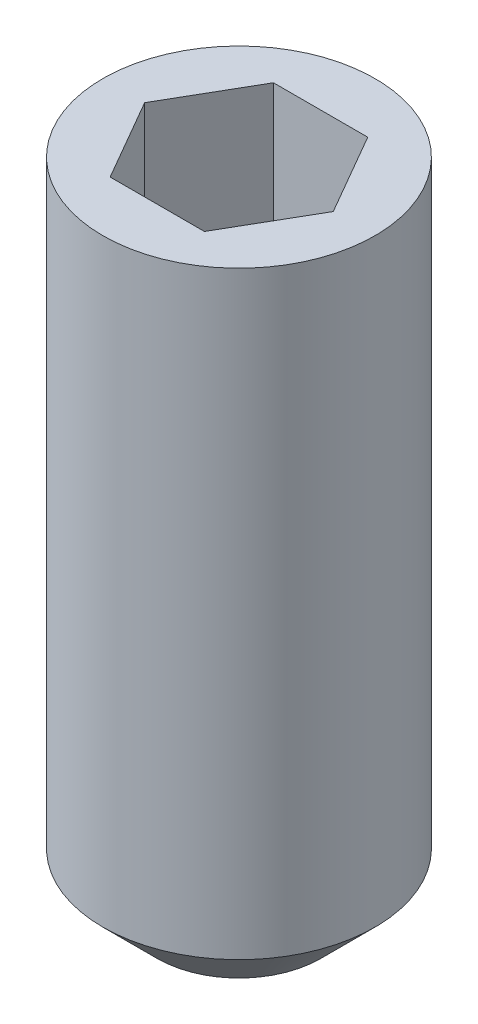
SolidWorks part; units mm, degrees
ref_plane "Front Plane" through (0, 0, 0) normal (0, 0, 1) x (1, 0, 0)
ref_plane "Top Plane" through (0, 0, 0) normal (0, 1, 0) x (1, 0, 0)
ref_plane "Right Plane" through (0, 0, 0) normal (1, 0, 0) x (0, 0, -1)
sketch "Sketch1" plane through (0, 0, 0) normal (0, 1, 0) x (1, 0, 0)
  circle A0 centre (0, 0) radius 1.25
  dimension "D1" = 2.5
extrude "Boss-Extrude1" add sketch "Sketch1" along normal blind 6
chamfer "Chamfer1" distance 0.5 angle 45 1 edges at (0, 0, 1.25)
sketch "Sketch2" plane through (0, 6, 0) normal (0, 1, 0) x (1, 0, 0)
  line L1 (0.433, -0.75) -> (0.866, 0)
  line L2 (0.866, 0) -> (0.433, 0.75)
  line L3 (0.433, 0.75) -> (-0.433, 0.75)
  line L4 (-0.433, 0.75) -> (-0.866, 0)
  line L5 (-0.866, 0) -> (-0.433, -0.75)
  line L6 (-0.433, -0.75) -> (0.433, -0.75)
  circle A0 centre (0, 0) radius 0.75 construction
  dimension "D1" = 1.5
extrude "Cut-Extrude1" cut sketch "Sketch2" against normal blind 1.5
